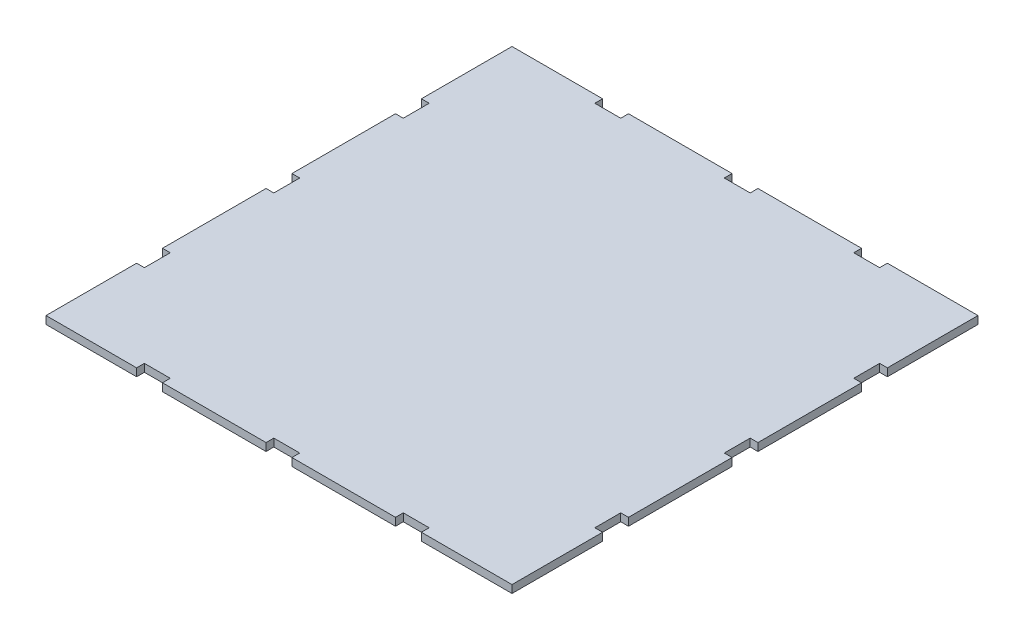
SolidWorks part; units mm, degrees
ref_plane "Front Plane" through (0, 0, 0) normal (0, 0, 1) x (1, 0, 0)
ref_plane "Top Plane" through (0, 0, 0) normal (0, 1, 0) x (1, 0, 0)
ref_plane "Right Plane" through (0, 0, 0) normal (1, 0, 0) x (0, 0, -1)
sketch "Sketch1" plane through (0, 0, 0) normal (0, 1, 0) x (1, 0, 0)
  line L1 (-90, 90) -> (90, 90)
  line L2 (-90, 90) -> (-90, -90)
  line L3 (-90, -90) -> (90, -90)
  line L4 (90, 90) -> (90, -90)
  line L5 (-90, 90) -> (90, -90) construction
  line L6 (-90, -90) -> (90, 90) construction
  point P0 (0, 0)
  dimension "D1" = 180
  dimension "D2" = 180
extrude "Boss-Extrude1" add sketch "Sketch1" along normal blind 3
sketch "Sketch2" plane through (0, 3, 0) normal (0, 1, 0) x (1, 0, 0)
  line L0 (0, 90) -> (0, -90) construction
  line L2 (0, 0) -> (90, 0) construction
  line L3 (90, -90) -> (90, 90) construction
  line L4 (0, 0) -> (-90, 0) construction
  line L5 (-90, 90) -> (-90, -90) construction
  line L6 (90, 90) -> (-90, 90) construction
  line L7 (-90, -90) -> (90, -90) construction
  line L8 (0, 90) -> (5, 90)
  line L9 (0, 90) -> (0, 87)
  line L10 (0, 87) -> (5, 87)
  line L11 (5, 90) -> (5, 87)
  line L12 (0, 90) -> (-5, 90)
  line L13 (0, 90) -> (0, 87)
  line L14 (0, 87) -> (-5, 87)
  line L15 (-5, 90) -> (-5, 87)
  line M5 (90, 90) -> (-90, 90)
  dimension "D1" = 3
  dimension "D2" = 5
  dimension "D3" = 5
extrude "Cut-Extrude1" cut sketch "Sketch2" against normal blind 3 contours L15 L14 L9 M5 | L11 L9 L10 M5
sketch "Sketch4" plane through (0, 3, 0) normal (0, 1, 0) x (1, 0, 0)
  line L0 (0, 87) -> (0, 0) construction
  line L1 (5, 87) -> (-5, 87) construction
  line L2 (0, 0) -> (0, -90) construction
  line L3 (-90, -90) -> (90, -90) construction
  line L4 (0, -90) -> (0, 0) construction
  line L6 (0, -90) -> (5, -90)
  line L7 (0, -90) -> (0, -87)
  line L8 (0, -87) -> (5, -87)
  line L9 (5, -90) -> (5, -87)
  line L10 (0, -90) -> (-5, -90)
  line L11 (0, -90) -> (0, -87)
  line L12 (0, -87) -> (-5, -87)
  line L13 (-5, -90) -> (-5, -87)
  line M10 (-90, -90) -> (90, -90)
  dimension "D1" = 5
  dimension "D2" = 3
  dimension "D3" = 5
extrude "Cut-Extrude2" cut sketch "Sketch4" against normal blind 3 contours L13 L7 L12 M10 | L9 L8 L7 M10
sketch "Sketch5" plane through (0, 3, 0) normal (0, 1, 0) x (1, 0, 0)
  line L0 (0, 87) -> (0, -87) construction
  line L1 (5, 87) -> (-5, 87) construction
  line L2 (5, -87) -> (-5, -87) construction
  line L4 (0, 0) -> (-90, 0)
  line L5 (-90, 90) -> (-90, -90) construction
  line L6 (90, 0) -> (0, 0)
  line L7 (90, -90) -> (90, 90) construction
  line L8 (-90, 0) -> (-87, 0)
  line L9 (-90, 0) -> (-90, -5)
  line L10 (-90, 0) -> (-87, 0)
  line L11 (-90, 0) -> (-90, 5)
  line L12 (-90, 5) -> (-87, 5)
  line L13 (-87, 0) -> (-87, 5)
  line L14 (-90, -5) -> (-87, -5)
  line L15 (-87, 0) -> (-87, -5)
  line M19 (-90, 90) -> (-90, -90)
  dimension "D1" = 3
  dimension "D2" = 5
  dimension "D3" = 5
extrude "Cut-Extrude3" cut sketch "Sketch5" against normal blind 3 contours L4 L13 L12 M19 | L15 L4 L14 M19
sketch "Sketch6" plane through (0, 3, 0) normal (0, 1, 0) x (1, 0, 0)
  line L0 (90, 0) -> (0, 0) construction
  line L1 (90, -90) -> (90, 90) construction
  line L2 (0, 0) -> (-87, 0) construction
  line L3 (-87, -5) -> (-87, 5) construction
  line L4 (-87, 0) -> (-87, 80) construction
  line L6 (90, 0) -> (87, 0)
  line L7 (90, 0) -> (90, 5)
  line L8 (90, 5) -> (87, 5)
  line L9 (87, 0) -> (87, 5)
  line L10 (90, 0) -> (87, 0)
  line L11 (90, 0) -> (90, -5)
  line L12 (90, -5) -> (87, -5)
  line L13 (87, 0) -> (87, -5)
  line M14 (90, -90) -> (90, 90)
  dimension "D1" = 3
  dimension "D2" = 5
  dimension "D3" = 5
extrude "Cut-Extrude4" cut sketch "Sketch6" against normal blind 3 contours L9 L6 L8 M14 | L6 L13 L12 M14
sketch "Sketch7" plane through (0, 3, 0) normal (0, 1, 0) x (1, 0, 0)
  line L0 (0, 0) -> (-87, 0)
  line L1 (-87, -5) -> (-87, 5) construction
  line L2 (-87, 0) -> (0, 0)
  line L3 (0, 0) -> (87, 0)
  line L4 (87, -5) -> (87, 5) construction
  line L5 (0, 0) -> (0, 87)
  line L6 (5, 87) -> (-5, 87) construction
  line L7 (0, 87) -> (0, 0)
  line L8 (0, -87) -> (0, 0)
  line L9 (5, -87) -> (-5, -87) construction
  line L10 (-90, -5) -> (-90, -45)
  line L11 (-5, 87) -> (-45, 87)
  line L12 (-90, -5) -> (-90, -90) construction
  line L14 (-5, 90) -> (-90, 90) construction
  line L15 (-90, -90) -> (-5, -90) construction
  line L16 (90, -5) -> (90, -45)
  line L17 (90, -90) -> (90, -5) construction
  line L18 (90, 5) -> (90, 45)
  line L19 (90, 5) -> (90, 90) construction
  line L20 (-90, 5) -> (-90, 45)
  line L21 (-90, 90) -> (-90, 5) construction
  line L22 (5, 87) -> (45, 87)
  line L23 (-5, -87) -> (-45, -87)
  line L24 (5, -87) -> (45, -87)
  line L25 (5, -90) -> (90, -90) construction
  line L26 (-90, -45) -> (-87, -45)
  line L27 (-90, -45) -> (-90, -55)
  line L28 (-90, -55) -> (-87, -55)
  line L29 (-87, -45) -> (-87, -55)
  line L30 (-45, -90) -> (-55, -90)
  line L31 (-45, -90) -> (-45, -87)
  line L32 (-45, -87) -> (-55, -87)
  line L33 (-55, -90) -> (-55, -87)
  line L34 (45, -90) -> (55, -90)
  line L35 (45, -90) -> (45, -87)
  line L36 (45, -87) -> (55, -87)
  line L37 (55, -90) -> (55, -87)
  line L38 (90, 90) -> (5, 90) construction
  line L39 (-45, 90) -> (-55, 90)
  line L40 (-45, 90) -> (-45, 87)
  line L41 (-45, 87) -> (-55, 87)
  line L42 (-55, 90) -> (-55, 87)
  line L43 (45, 90) -> (55, 90)
  line L44 (45, 90) -> (45, 87)
  line L45 (45, 87) -> (55, 87)
  line L46 (55, 90) -> (55, 87)
  line L47 (90, -45) -> (87, -45)
  line L48 (-90, 45) -> (-87, 45)
  line L49 (-90, 45) -> (-90, 55)
  line L50 (-90, 55) -> (-87, 55)
  line L51 (-87, 45) -> (-87, 55)
  line L52 (90, 45) -> (87, 45)
  line L53 (90, 45) -> (90, 55)
  line L54 (90, 55) -> (87, 55)
  line L55 (87, 45) -> (87, 55)
  line L56 (90, -45) -> (90, -55)
  line L57 (90, -55) -> (87, -55)
  line L58 (87, -45) -> (87, -55)
  line M19 (90, 90) -> (5, 90)
  line M29 (-90, -90) -> (-5, -90)
  line M33 (5, -90) -> (90, -90)
  line M34 (90, -90) -> (90, -5)
  dimension "D1" = 40
  dimension "D2" = 40
  dimension "D3" = 40
  dimension "D4" = 40
  dimension "D5" = 40
  dimension "D6" = 40
  dimension "D7" = 10
  dimension "D8" = 10
  dimension "D9" = 10
  dimension "D10" = 10
extrude "Cut-Extrude5" cut sketch "Sketch7" against normal blind 10 contours L33 L31 L32 M29 | L37 L36 L35 M33 | L47 L58 L57 M34 | L46 L44 L45 M19 | L27 L28 L29 L26 | L52 L55 L54 L53 | L49 L50 L51 L48 | L40 L39 L42 L41
